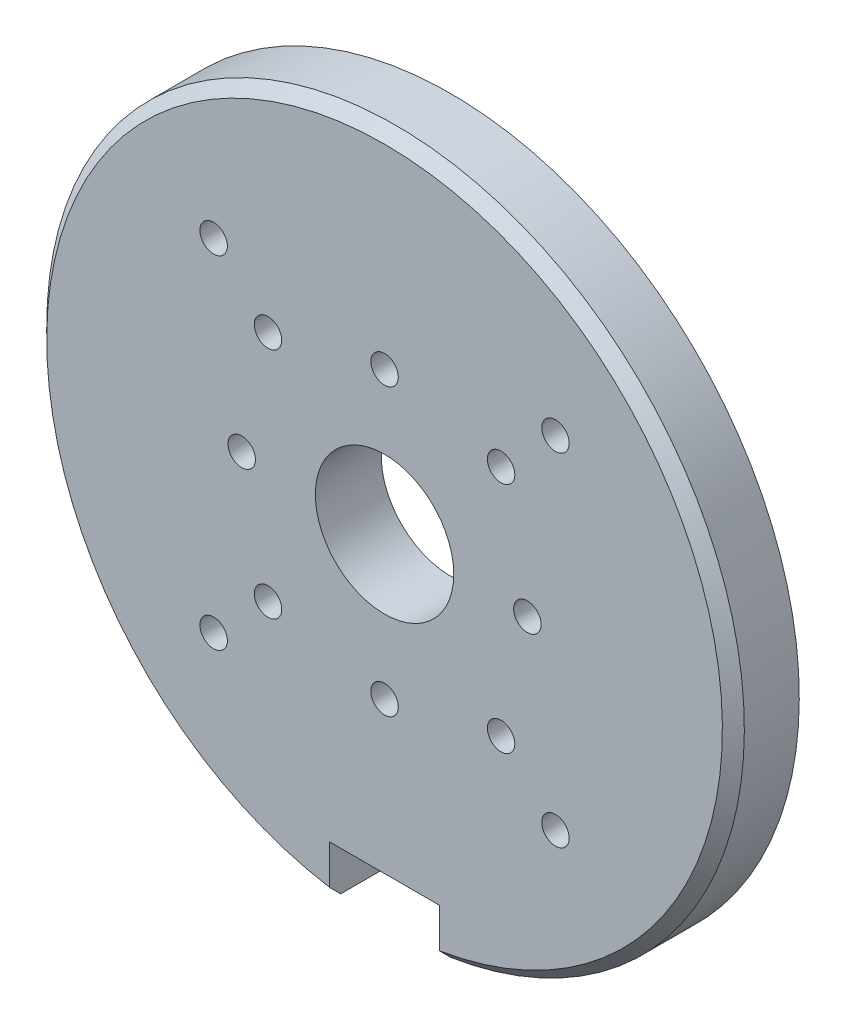
SolidWorks part; units mm, degrees
material "Сплав 2024"
ref_plane "Спереди" through (0, 0, 0) normal (0, 0, 1) x (1, 0, 0)
ref_plane "Сверху" through (0, 0, 0) normal (0, 1, 0) x (1, 0, 0)
ref_plane "Справа" through (0, 0, 0) normal (1, 0, 0) x (0, 0, -1)
sketch "Эскиз1" plane through (0, 0, 0) normal (0, 0, 1) x (1, 0, 0)
  circle A0 centre (0, 0) radius 31.75
  dimension "D1" = 63.5
extrude "Бобышка-Вытянуть1" add sketch "Эскиз1" along normal blind 6
sketch "Эскиз2" plane through (0, 0, 6) normal (0, 0, 1) x (1, 0, 0)
  line L0 (0, 13) -> (0, 0) construction
  line L1 (-13, 0) -> (13, 0) construction
  line L3 (0, 0) -> (0, -31.75) construction
  line L5 (-5, -26.75) -> (5, -26.75)
  line L6 (-5, -26.75) -> (-5, -36.75)
  line L7 (-5, -36.75) -> (5, -36.75)
  line L8 (5, -26.75) -> (5, -36.75)
  line L9 (-5, -26.75) -> (5, -36.75) construction
  line L10 (-5, -36.75) -> (5, -26.75) construction
  circle A0 centre (0, 0) radius 13 construction
  circle A1 centre (0, 0) radius 31.75 construction
  dimension "D1" = 26
  dimension "D4" = 10
  dimension "D5" = 10
extrude "Вырез-Вытянуть1" cut sketch "Эскиз2" against normal through all
hole_wizard "Отверстие обработанное метчиком M3x0.52" positions "Эскиз4" profile "Эскиз3" tap size "M3x0.5" standard "Ansi Metric" end condition through all
sketch "Эскиз4" plane through (0, 0, 6) normal (0, 0, 1) x (1, 0, 0)
  line L1 (0, 0) -> (0, -31.75) construction
  circle A3 centre (0, 0) radius 13 construction
  point P0 (0, 13)
  point P3 (13, 0)
  point P6 (-13, 0)
  point P9 (0, -13)
sketch "Эскиз3" plane through (0, 13, 6) normal (1, 0, 0) x (0, -1, 0)
  line L0 (0, 0) -> (0, 6)
  line L1 (0, 6) -> (1.25, 6)
  line L2 (1.25, 6) -> (1.25, 0)
  line L5 (1.25, 0) -> (0, 0)
  line L11 (0, -6.35) -> (0, 107.95) construction
  dimension "Диаметр проходного сверла" = 2.5
  dimension "Глубина проходного сверла" = 6
cosmetic thread "Отверстие резьбы1" parameters "D2"=3
cosmetic thread "Отверстие резьбы2" parameters "D2"=3
cosmetic thread "Отверстие резьбы3" parameters "D2"=3
cosmetic thread "Отверстие резьбы12" parameters "D2"=3
sketch "Эскиз5" plane through (0, 0, 6) normal (0, 0, 1) x (1, 0, 0)
  line L0 (-15.5563, 15.5563) -> (15.5563, -15.5563) construction
  line L1 (15.5563, 15.5563) -> (-15.5563, -15.5563) construction
  line L2 (0, 13) -> (0, 0) construction
  circle A0 centre (0, 0) radius 15 construction
  circle A1 centre (0, 0) radius 22 construction
  dimension "D1" = 30
  dimension "D4" = 44
  dimension "D2" = 45
  dimension "D3" = 90
hole_wizard "Отверстие обработанное метчиком M3x0.51" positions "Эскиз7" profile "Эскиз6" tap size "M3x0.5" standard "Ansi Metric" end condition through all
sketch "Эскиз7" plane through (0, 0, 6) normal (0, 0, 1) x (1, 0, 0)
  line L0 (15.5563, 15.5563) -> (-15.5563, -15.5563) construction
  line L1 (-15.5563, 15.5563) -> (15.5563, -15.5563) construction
  circle A0 centre (0, 0) radius 15 construction
  point P0 (-15.5563, 15.5563)
  point P3 (-15.5563, -15.5563)
  point P6 (15.5563, -15.5563)
  point P9 (15.5563, 15.5563)
  point P12 (10.6066, 10.6066)
  point P18 (-10.6066, 10.6066)
  point P22 (-10.6066, -10.6066)
  point P24 (10.6066, -10.6066)
sketch "Эскиз6" plane through (-15.5563, 15.5563, 6) normal (1, 0, 0) x (0, -1, 0)
  line L0 (0, 0) -> (0, 6)
  line L1 (0, 6) -> (1.25, 6)
  line L2 (1.25, 6) -> (1.25, 0)
  line L5 (1.25, 0) -> (0, 0)
  line L11 (0, -6.35) -> (0, 107.95) construction
  dimension "Диаметр проходного сверла" = 2.5
  dimension "Глубина проходного сверла" = 6
cosmetic thread "Отверстие резьбы4" parameters "D2"=3
cosmetic thread "Отверстие резьбы5" parameters "D2"=3
cosmetic thread "Отверстие резьбы6" parameters "D2"=3
cosmetic thread "Отверстие резьбы7" parameters "D2"=3
cosmetic thread "Отверстие резьбы8" parameters "D2"=3
cosmetic thread "Отверстие резьбы9" parameters "D2"=3
cosmetic thread "Отверстие резьбы10" parameters "D2"=3
cosmetic thread "Отверстие резьбы11" parameters "D2"=3
sketch "Эскиз8" plane through (0, 0, 6) normal (0, 0, 1) x (1, 0, 0)
  circle A0 centre (0, 0) radius 6.3
  dimension "D1" = 12.6
extrude "Вырез-Вытянуть2" cut sketch "Эскиз8" against normal through all
chamfer "Фаска1" distance 1 angle 45 1 edges at (0, 31.75, 6)
